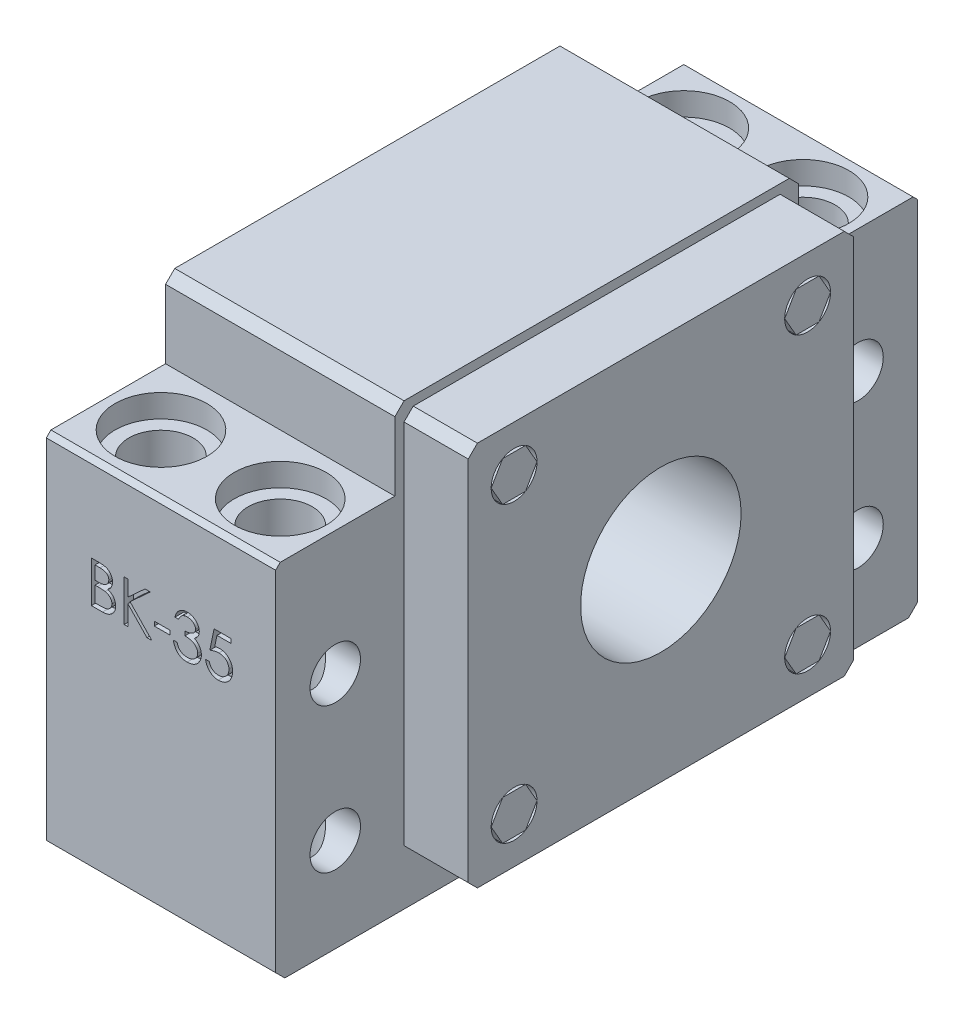
SolidWorks part; units mm, degrees
ref_plane "Front Plane" through (0, 0, 0) normal (0, 0, 1) x (1, 0, 0)
ref_plane "Top Plane" through (0, 0, 0) normal (0, 1, 0) x (1, 0, 0)
ref_plane "Right Plane" through (0, 0, 0) normal (1, 0, 0) x (0, 0, -1)
sketch "Sketch1" plane through (0, 0, 0) normal (1, 0, 0) x (0, 0, -1)
  line L0 (-68, 0) -> (68, 0)
  line L1 (70, 2) -> (70, 78)
  line L2 (69, 79) -> (44, 79)
  line L3 (44, 79) -> (44, 94)
  line L4 (42, 96) -> (-42, 96)
  line L5 (-44, 94) -> (-44, 79)
  line L6 (-44, 79) -> (-69, 79)
  line L7 (-70, 78) -> (-70, 2)
  line L8 (0, -15.4829) -> (0, 101.6761) construction
  line L9 (-42, 96) -> (-44, 94)
  line L10 (44, 94) -> (42, 96)
  line L11 (68, 0) -> (70, 2)
  line L12 (-70, 2) -> (-68, 0)
  line L13 (-69, 79) -> (-70, 78)
  line L14 (70, 78) -> (69, 79)
  circle A0 centre (0, 52) radius 17.5
  point P0 (-70, 0)
  point P1 (70, 0)
  point P3 (70, 79)
  point P6 (44, 96)
  point P7 (-44, 96)
  point P9 (-70, 79)
  dimension "D8" = 35
  dimension "D1" = 140
  dimension "D2" = 70
  dimension "D3" = 88
  dimension "D4" = 44
  dimension "D5" = 96
  dimension "D6" = 79
  dimension "D7" = 79
  dimension "D9" = 52
extrude "Boss-Extrude1" add sketch "Sketch1" along normal mid plane 50
sketch "Sketch2" plane through (25, 0, 0) normal (1, 0, 0) x (0, 0, -1)
  line L0 (44, 79) -> (44, 94) construction
  line L1 (-40, 94) -> (40, 94)
  line L2 (-42, 92) -> (-42, 12)
  line L3 (-40, 10) -> (40, 10)
  line L4 (42, 92) -> (42, 12)
  line L5 (-44, 94) -> (-44, 79) construction
  line L6 (42, 96) -> (-42, 96) construction
  line L7 (-42, 92) -> (-40, 94)
  line L8 (40, 94) -> (42, 92)
  line L9 (40, 10) -> (42, 12)
  line L10 (-42, 12) -> (-40, 10)
  circle A0 centre (0, 52) radius 17.5
  point P0 (-42, 94)
  point P1 (42, 10)
  point P2 (-42, 10)
  point P3 (42, 94)
  point P6 (-44, 86.5)
  dimension "D1" = 2
  dimension "D2" = 2
  dimension "D3" = 2
  dimension "D4" = 84
extrude "Boss-Extrude2" add sketch "Sketch2" along normal blind 14
sketch "Sketch4" plane through (0, 79, 0) normal (0, 1, 0) x (1, 0, 0)
  line L0 (0, -75.5575) -> (0, 75.5575) construction
  line L4 (25, 69) -> (25, 44) construction
  circle A0 centre (-13, 57) radius 10
  circle A1 centre (13, 57) radius 10
  circle A2 centre (13, -57) radius 10
  circle A3 centre (-13, -57) radius 10
  dimension "D6" = 20
  dimension "D3" = 12
extrude "Cut-Extrude2" cut sketch "Sketch4" against normal blind 5
sketch "Sketch5" plane through (0, 74, 0) normal (0, 1, 0) x (1, 0, 0)
  circle A0 centre (-13, -57) radius 7
  circle A1 centre (13, -57) radius 7
  circle A2 centre (-13, 57) radius 7
  circle A3 centre (13, 57) radius 7
  dimension "D1" = 14
  dimension "D2" = 14
  dimension "D3" = 14
  dimension "D4" = 14
extrude "Cut-Extrude3" cut sketch "Sketch5" against normal through all
sketch "Sketch6" plane through (25, 0, 0) normal (1, 0, 0) x (0, 0, -1)
  line L1 (0, 52) -> (-93.5766, 52) construction
  line L4 (-89.9537, 20.4464) -> (-21.1173, 20.4464) construction
  circle A0 centre (-57, 52) radius 5.5
  circle A1 centre (-57, 20.4464) radius 5.5
  circle A2 centre (57, 20.4464) radius 5.5
  circle A3 centre (57, 52) radius 5.5
  dimension "D3" = 11
  dimension "D4" = 11
extrude "Cut-Extrude4" cut sketch "Sketch6" against normal blind 13
sketch "Sketch7" plane through (0, 0, 70) normal (0, 0, 1) x (1, 0, 0)
  text T0 "BK-35" font "Century Gothic" height 9
extrude "Cut-Extrude5" cut sketch "Sketch7" against normal blind 2
sketch "Sketch8" plane through (25, 0, 0) normal (1, 0, 0) x (0, 0, -1)
  text T0 "Şahin Rulman" font "Century Gothic" height 5
extrude "Cut-Extrude6" cut sketch "Sketch8" against normal blind 2
sketch "Sketch9" plane through (39, 0, 0) normal (1, 0, 0) x (0, 0, -1)
  line L0 (-40, 10) -> (40, 10) construction
  line L1 (-42, 92) -> (-42, 12) construction
  line L3 (40, 94) -> (-40, 94) construction
  line L4 (40, 94) -> (-40, 94) construction
  line L5 (42, 12) -> (42, 92) construction
  circle A0 centre (-32, 84) radius 5
  circle A1 centre (32, 84) radius 5
  circle A2 centre (32, 20) radius 5
  circle A3 centre (-32, 20) radius 5
  point P14 (-73.1414, 88.3353)
  dimension "D1" = 10
  dimension "D2" = 10
  dimension "D3" = 10
  dimension "D4" = 10
  dimension "D5" = 10
  dimension "D6" = 10
  dimension "D7" = 10
  dimension "D8" = 10
  dimension "D9" = 10
extrude "Cut-Extrude7" cut sketch "Sketch9" against normal up to surface (14 mm away) up to face at (25, 5.0375, -17.0123)
sketch "Sketch10" plane through (39, 0, 0) normal (1, 0, 0) x (0, 0, -1)
  line L1 (-27, 84) -> (-29.5, 88.3301)
  line L2 (-29.5, 88.3301) -> (-34.5, 88.3301)
  line L3 (-34.5, 88.3301) -> (-37, 84)
  line L4 (-37, 84) -> (-34.5, 79.6699)
  line L5 (-34.5, 79.6699) -> (-29.5, 79.6699)
  line L6 (-29.5, 79.6699) -> (-27, 84)
  line L7 (37, 84) -> (34.5, 88.3301)
  line L8 (34.5, 88.3301) -> (29.5, 88.3301)
  line L9 (29.5, 88.3301) -> (27, 84)
  line L10 (27, 84) -> (29.5, 79.6699)
  line L11 (29.5, 79.6699) -> (34.5, 79.6699)
  line L12 (34.5, 79.6699) -> (37, 84)
  line L13 (37, 20) -> (34.5, 24.3301)
  line L14 (34.5, 24.3301) -> (29.5, 24.3301)
  line L15 (29.5, 24.3301) -> (27, 20)
  line L16 (27, 20) -> (29.5, 15.6699)
  line L17 (29.5, 15.6699) -> (34.5, 15.6699)
  line L18 (34.5, 15.6699) -> (37, 20)
  line L19 (-27, 20) -> (-29.5, 24.3301)
  line L20 (-29.5, 24.3301) -> (-34.5, 24.3301)
  line L21 (-34.5, 24.3301) -> (-37, 20)
  line L22 (-37, 20) -> (-34.5, 15.6699)
  line L23 (-34.5, 15.6699) -> (-29.5, 15.6699)
  line L24 (-29.5, 15.6699) -> (-27, 20)
  circle A0 centre (-32, 84) radius 4.3301 construction
  circle A1 centre (32, 84) radius 4.3301 construction
  circle A2 centre (32, 20) radius 4.3301 construction
  circle A3 centre (-32, 20) radius 4.3301 construction
extrude "Boss-Extrude3" add sketch "Sketch10" against normal up to surface (14 mm away) separate body up to face at (25, 5.0375, -17.0123)
